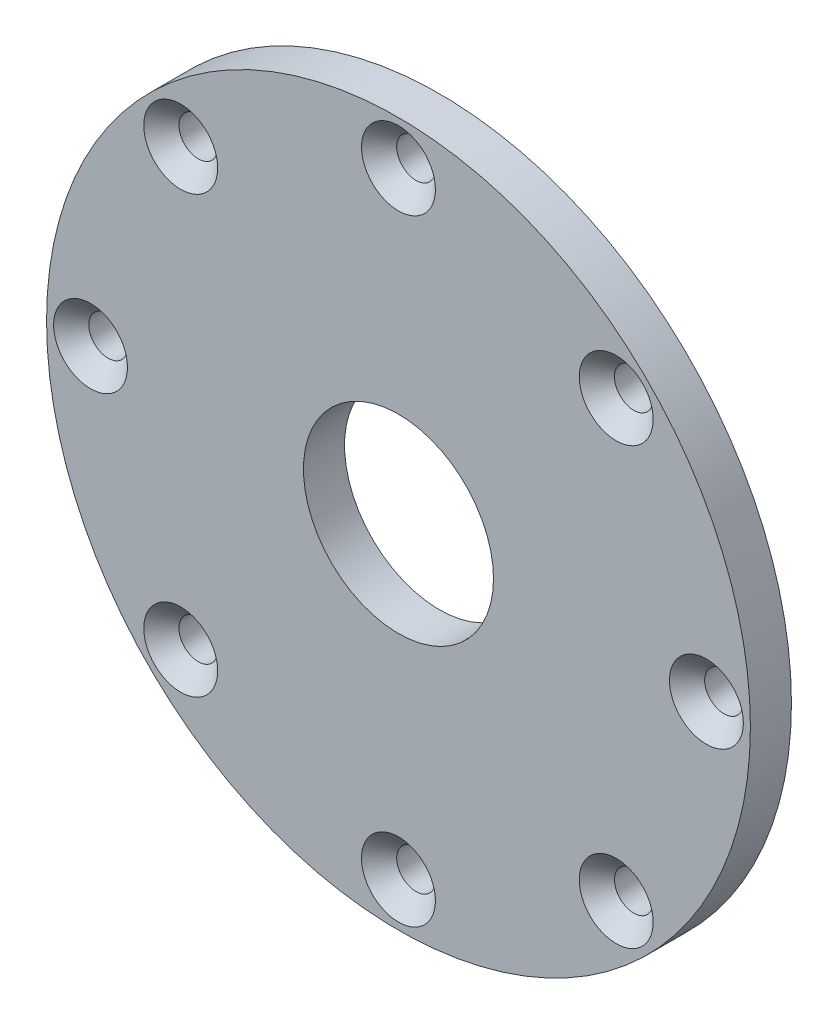
SolidWorks part; units mm, degrees
ref_plane "Front Plane" through (0, 0, 0) normal (0, 0, 1) x (1, 0, 0)
ref_plane "Top Plane" through (0, 0, 0) normal (0, 1, 0) x (1, 0, 0)
ref_plane "Right Plane" through (0, 0, 0) normal (1, 0, 0) x (0, 0, -1)
sketch "Sketch1" plane through (0, 0, 0) normal (0, 0, 1) x (1, 0, 0)
  circle A0 centre (0, 0) radius 60
  circle A1 centre (0, 0) radius 16.2
  dimension "D1" = 120
  dimension "D2" = 32.4
extrude "Boss-Extrude1" add sketch "Sketch1" along normal blind 7
sketch "Sketch2" plane through (0, 0, 7) normal (0, 0, 1) x (1, 0, 0)
  circle A0 centre (0, 0) radius 52.5
  circle A1 centre (0, 0) radius 60 construction
  point P5 (0, 52.5)
  point P8 (37.1231, 37.1231)
  point P9 (52.5, 0)
  point P10 (37.1231, -37.1231)
  point P11 (0, -52.5)
  point P12 (-37.1231, -37.1231)
  point P13 (-52.5, 0)
  point P14 (-37.1231, 37.1231)
  dimension "D1" = 7.5
  dimension "D2" = 8
hole_wizard "CSK for M6 Countersunk Flat Head Screw1" positions "Sketch2" profile "Sketch3" countersink size "M6" standard "ISO" end condition through all
sketch "Sketch3" plane through (-37.1231, 37.1231, 7) normal (1, 0, 0) x (0, -1, 0)
  line L0 (0, 0) -> (0, 7)
  line L1 (0, 7) -> (3.3, 7)
  line L2 (3.3, 7) -> (3.3, 3)
  line L3 (3.3, 3) -> (6.3, 0)
  line L5 (6.3, 0) -> (0, 0)
  line L6 (-3.3, 3) -> (-6.3, 0) construction
  line L11 (0, -6.35) -> (0, 107.95) construction
  dimension "Thru Hole Dia." = 6.6
  dimension "Thru Hole Depth" = 7
  dimension "Near C'Sink Dia." = 12.6
  dimension "Near C'Sink Angle" = 90
